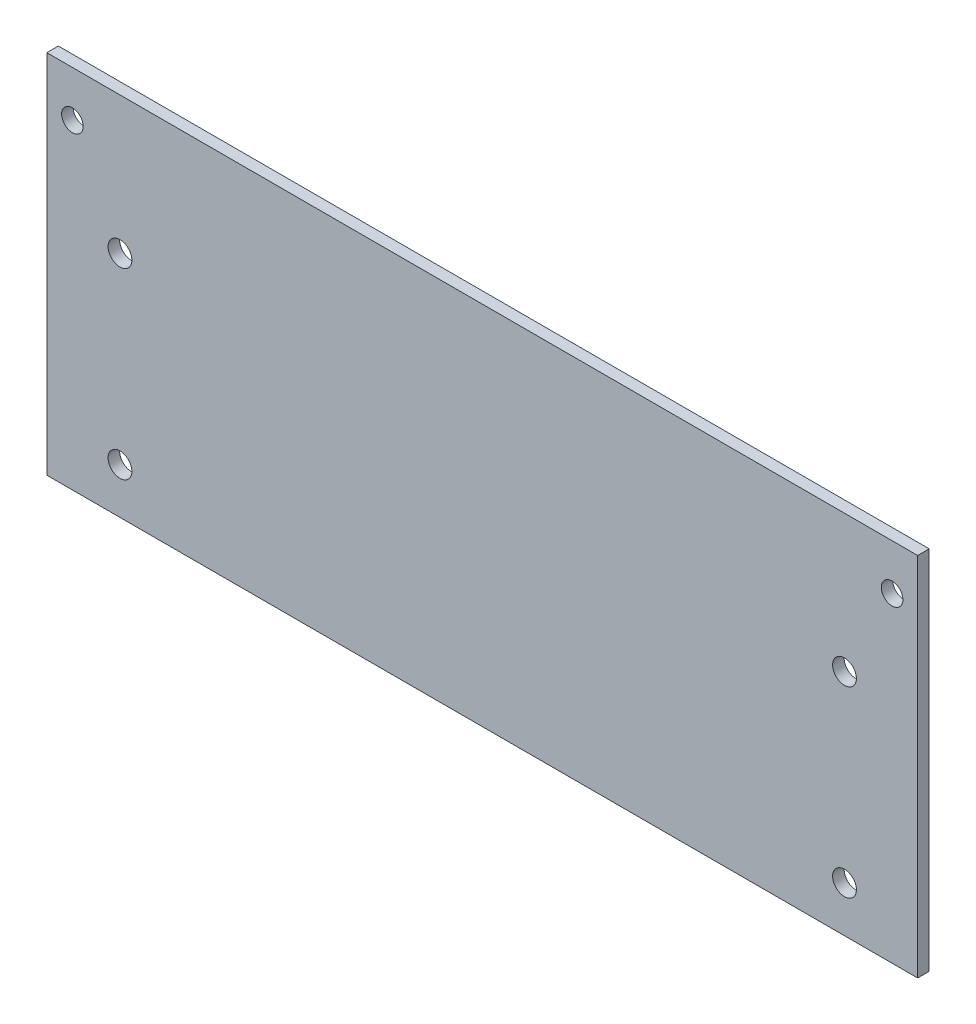
SolidWorks part; units mm, degrees
ref_plane "Front Plane" through (0, 0, 0) normal (0, 0, 1) x (1, 0, 0)
ref_plane "Top Plane" through (0, 0, 0) normal (0, 1, 0) x (1, 0, 0)
ref_plane "Right Plane" through (0, 0, 0) normal (1, 0, 0) x (0, 0, -1)
sketch "Sketch1" plane through (0, 0, 0) normal (0, 0, 1) x (1, 0, 0)
  line L0 (60.452, 19.05) -> (60.452, 31.75)
  line L1 (-50.292, -12.7) -> (50.292, -12.7) construction
  line L2 (-50.292, -12.7) -> (-50.292, 12.7) construction
  line L3 (-50.292, 12.7) -> (50.292, 12.7) construction
  line L4 (50.292, -12.7) -> (50.292, 12.7) construction
  line L5 (-50.292, -12.7) -> (50.292, 12.7) construction
  line L6 (-50.292, 12.7) -> (50.292, -12.7) construction
  line L7 (-60.452, -19.05) -> (60.452, -19.05)
  line L8 (-60.452, -19.05) -> (-60.452, 19.05)
  line L10 (60.452, -19.05) -> (60.452, 19.05)
  line L11 (-60.452, -19.05) -> (60.452, 19.05) construction
  line L12 (-60.452, 19.05) -> (60.452, -19.05) construction
  line L13 (60.452, 31.75) -> (-60.452, 31.75)
  line L14 (-60.452, 31.75) -> (-60.452, 19.05)
  line L15 (67.056, 12.7) -> (67.056, 41.1152) construction
  line L16 (67.056, 20.574) -> (85.9229, 20.574) construction
  line L17 (67.056, 33.274) -> (84.5094, 33.274) construction
  line L18 (67.056, 25.4) -> (56.896, 25.4) construction
  line L19 (-67.056, 12.7) -> (-67.056, 37.6872) construction
  line L21 (56.896, 25.4) -> (-74.3167, 25.4) construction
  circle A0 centre (-50.292, 12.7) radius 1.651
  circle A1 centre (-50.292, -12.7) radius 1.651
  circle A2 centre (50.292, 12.7) radius 1.651
  circle A3 centre (50.292, -12.7) radius 1.651
  circle A4 centre (56.896, 25.4) radius 1.4986
  circle A5 centre (-56.896, 25.4) radius 1.4986
  point P0 (0, 0)
  point P10 (0, 0)
  dimension "D3" = 3.302
  dimension "D4" = 3.302
  dimension "D5" = 3.302
  dimension "D6" = 3.302
  dimension "D14" = 2.9972
  dimension "D17" = 2.9972
  dimension "D1" = 100.584
  dimension "D2" = 25.4
  dimension "D7" = 6.35
  dimension "D8" = 10.16
  dimension "D9" = 19.05
  dimension "D10" = 16.764
  dimension "D11" = 7.874
  dimension "D12" = 12.7
  dimension "D13" = 10.16
  dimension "D15" = 16.764
  dimension "D16" = 10.16
  dimension "D18" = 12.7
  dimension "D19" = 10.16
extrude "Boss-Extrude1" add sketch "Sketch1" along normal blind 1.6
